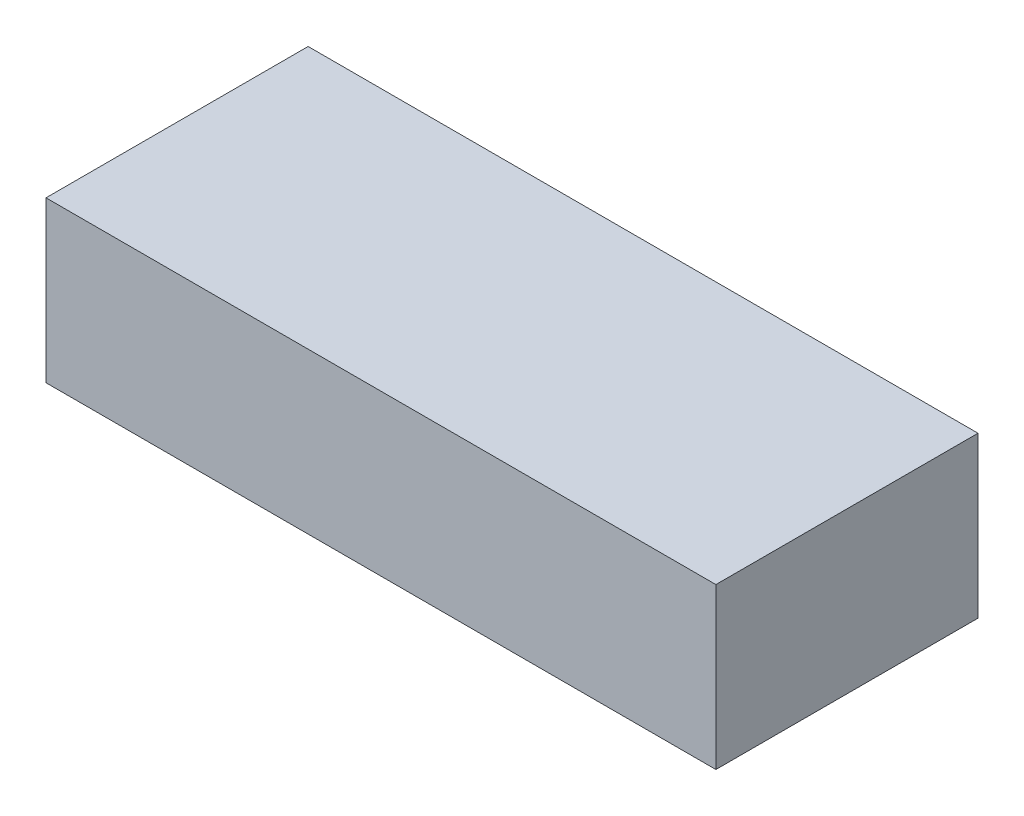
SolidWorks part; units mm, degrees
ref_plane "Front Plane" through (0, 0, 0) normal (0, 0, 1) x (1, 0, 0)
ref_plane "Top Plane" through (0, 0, 0) normal (0, 1, 0) x (1, 0, 0)
ref_plane "Right Plane" through (0, 0, 0) normal (1, 0, 0) x (0, 0, -1)
sketch "Sketch1" plane through (0, 0, 0) normal (0, 1, 0) x (1, 0, 0)
  line L1 (-6.9, -2.7) -> (6.9, -2.7)
  line L2 (-6.9, -2.7) -> (-6.9, 2.7)
  line L3 (-6.9, 2.7) -> (6.9, 2.7)
  line L4 (6.9, -2.7) -> (6.9, 2.7)
  line L5 (-6.9, -2.7) -> (6.9, 2.7) construction
  line L6 (-6.9, 2.7) -> (6.9, -2.7) construction
  point P0 (0, 0)
  dimension "D1" = 13.8
  dimension "D2" = 5.4
extrude "Boss-Extrude1" add sketch "Sketch1" along normal blind 3.3
